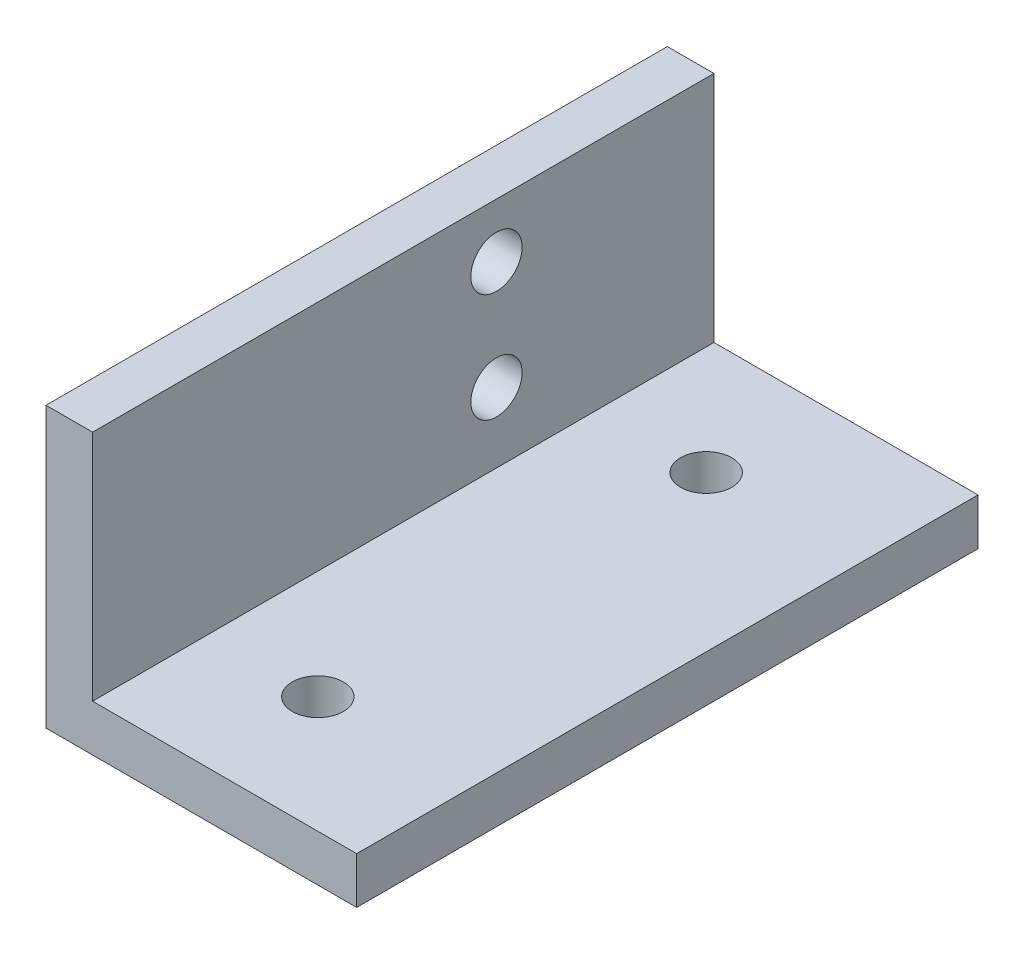
SolidWorks part; units mm, degrees
ref_plane "Plano frontal" through (0, 0, 0) normal (0, 0, 1) x (1, 0, 0)
ref_plane "Plano superior" through (0, 0, 0) normal (0, 1, 0) x (1, 0, 0)
ref_plane "Plano direito" through (0, 0, 0) normal (1, 0, 0) x (0, 0, -1)
sketch "Esboço1" plane through (0, 0, 0) normal (0, 0, 1) x (1, 0, 0)
  line L0 (20, 0) -> (0, 0)
  line L1 (0, 0) -> (0, 18)
  line L2 (20, 3) -> (3, 3)
  line L3 (3, 3) -> (3, 18)
  line L4 (20, 0) -> (20, 3)
  line L5 (0, 18) -> (3, 18)
  dimension "D2" = 20
  dimension "D3" = 18
  dimension "D1" = 3
extrude "Ressalto-extrusão1" add sketch "Esboço1" along normal blind 40
sketch "Esboço2" plane through (0, 0, 0) normal (0, -1, 0) x (1, 0, 0)
  line L0 (0, 20) -> (20, 20) construction
  line L1 (0, 40) -> (0, 0) construction
  line L2 (20, 40) -> (20, 0) construction
  circle A0 centre (10, 7.5) radius 1.65
  circle A1 centre (10, 32.5) radius 1.65
  dimension "D2" = 3.3
  dimension "D1" = 25
  dimension "D3" = 10
extrude "Corte-extrusão1" cut sketch "Esboço2" against normal blind 40
sketch "Esboço3" plane through (0, 0, 0) normal (-1, 0, 0) x (0, 0, 1)
  line L0 (0, 11) -> (19.0245, 11) construction
  line L1 (0, 18) -> (0, 0) construction
  line L2 (40, 0) -> (0, 0) construction
  line L3 (40, 18) -> (0, 18) construction
  circle A0 centre (14, 7.5) radius 1.65
  circle A1 centre (14, 14.5) radius 1.65
  point P10 (20, 0)
  dimension "D2" = 3.3
  dimension "D1" = 7
  dimension "D3" = 6
  dimension "D4" = 7
extrude "Corte-extrusão2" cut sketch "Esboço3" against normal blind 40
